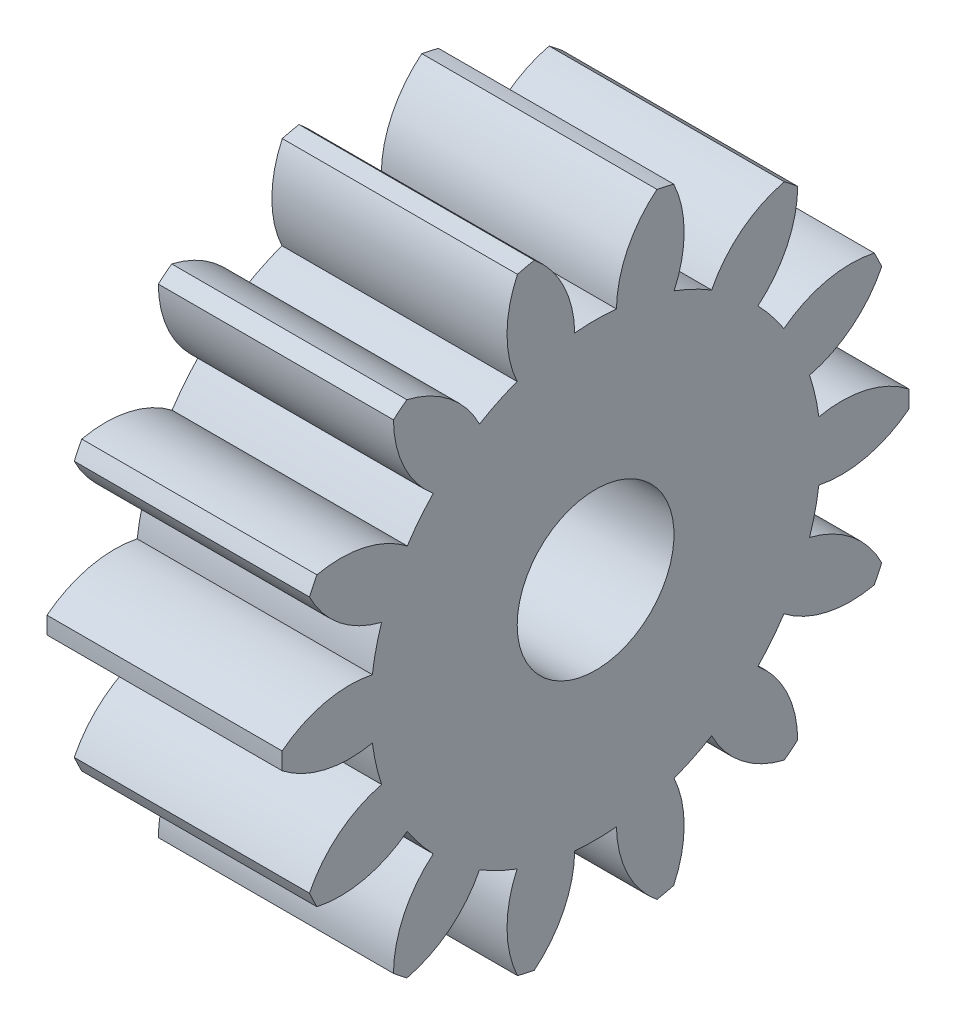
SolidWorks part; units mm, degrees
ref_plane "Plane1" through (0, 0, 0) normal (0, 0, 1) x (1, 0, 0)
ref_plane "Plane2" through (0, 0, 0) normal (0, 1, 0) x (1, 0, 0)
ref_plane "Plane3" through (0, 0, 0) normal (1, 0, 0) x (0, 0, -1)
sketch "HoldingSke" plane through (0, 0, 0) normal (0, 1, 0) x (1, 0, 0)
  line L0 (0, 0) -> (3.8812, -0.9677)
  line L1 (-15, 0) -> (100, 0) construction
  line L2 (0, 0) -> (-2.1039, 2.3779)
  line L3 (0, 0) -> (-11.863, 4.5341)
  line L4 (0, 0) -> (8.3795, 2.0892)
  line L5 (0, 0) -> (-46.8476, -17.4728)
  line L6 (0, 0) -> (-1.2434, -0.839)
  line L7 (-2.1039, 2.3779) -> (8.6586, 51.2059)
  line L8 (-76.2, 54.61) -> (-76.1, 54.61)
  line L9 (-71.009, 38.7566) -> (-53.1078, 45.2721)
  line L10 (-76.2, 71.12) -> (104.1128, 71.12)
  line L11 (0, 0) -> (-1.5, 0)
  line L12 (-76.2, 101.6) -> (-76.192, 101.6)
  line L13 (24.9733, 27.94) -> (52.9518, 28.4284)
  line L14 (24.9733, 27.94) -> (24.9743, 27.94)
  line L15 (24.9733, 27.94) -> (100.4006, 29.5858)
  line L16 (-63.627, -0.25) -> (-12.827, -0.25)
  circle A0 centre (0, 0) radius 0.5
  circle A1 centre (0, 0) radius 1.4365
  circle A2 centre (0, 0) radius 37.5
  circle A3 centre (0, 0) radius 0.5
  dimension "MHD" = 2.873
  dimension "Hub_dia" = 75
  dimension "Bore" = 1
  dimension "MBD" = 1
  dimension "Num_teeth" = 14
  dimension "Pitch" = 4
  dimension "Overall_len" = 50
  dimension "Show_teeth" = 14
  dimension "Thickness" = 1.5
  dimension "OAL" = 50.0001
  dimension "T_dim" = 0.1
  dimension "Ap" = 20
  dimension "H" = 19.05
  dimension "Pitch_radius" = 180.3128
  dimension "Width" = 1.5
  dimension "Backlash" = 0.008
  dimension "Addendum_fac" = 1
  dimension "Dedendum_fac" = 1.25
  dimension "Clearance_fac" = 0.25
  dimension "Dedendum_add" = 0.001
  dimension "Module" = 0.25
sketch "BasProSke" plane through (0, 0, 0) normal (0, 1, 0) x (1, 0, 0)
  line L0 (-10, 0) -> (60, 0) construction
  line L1 (0, 0) -> (0, 2)
  line L2 (0, 0) -> (1.5, 0)
  line L3 (1.5, 0) -> (1.5, 2)
  line L4 (1.5, 2) -> (0, 2)
  dimension "Thickness" = 1.5
  dimension "Diameter" = 4
revolve "Base-Revolve" add sketch "BasProSke" angle 360 about L0
sketch "TooCutSke" plane through (0, 0, 0) normal (1, 0, 0) x (0, 0, -1)
  line L1 (0, 0) -> (0, 107) construction
  line L2 (0, 0) -> (-0.2099, 1.7374) construction
  line L3 (0, 0) -> (-0.7746, 3.3938) construction
  line L4 (-0.2099, 1.7374) -> (-0.3873, 1.6969) construction
  arc A0 (0.1329, 1.4303) -> (-0.1329, 1.4303) centre (0, 0) ccw
  arc A1 (0.418, 1.9818) -> (-0.418, 1.9818) centre (0, 0) ccw
  circle A2 centre (0, 0) radius 1.75 construction
  circle A3 centre (0, 0) radius 1.6445 construction
  arc A4 (-0.1329, 1.4303) -> (-0.418, 1.9818) centre (-0.8328, 1.418) ccw
  arc A5 (0.418, 1.9818) -> (0.1329, 1.4303) centre (0.8328, 1.418) ccw
  dimension "Root_dia" = 2.873
  dimension "Overcut_dia" = 4.0508
  dimension "Pitch_dia" = 3.5
  dimension "Base_dia" = 3.2889
  dimension "Flank_rad" = 0.7
  dimension "Half_ang" = 12.857
  dimension "Half_CT" = 0.1819
extrude "ToothCut" cut sketch "TooCutSke" along normal through all
fillet "Breaks" [suppressed] radius 0.005
fillet "RootFillets" [suppressed] radius 0.0635
pattern_circular "TeethCuts" count 14 every 25.714 about axis through (-10, 0, 0) along (1, 0, 0) of "ToothCut", "RootFillets", "Breaks"
sketch "HubNeaOneSke" plane through (0, 0, 0) normal (-1, 0, 0) x (0, 0, 1)
  circle A0 centre (0, 0) radius 1.4365
  dimension "Diameter" = 2.873
extrude "HubNearOne" [suppressed] add sketch "HubNeaOneSke" along normal blind 48.5001
sketch "HubNeaBotSke" plane through (0, 0, 0) normal (-1, 0, 0) x (0, 0, 1)
  circle A0 centre (0, 0) radius 1.4365
  dimension "Diameter" = 2.873
extrude "HubNearBoth" [suppressed] add sketch "HubNeaBotSke" along normal blind 24.25
ref_plane "FarPln" through (1.5, 0, 0) normal (1, 0, 0) x (0, 0, -1)
sketch "HubFarSke" plane through (1.5, 0, 0) normal (1, 0, 0) x (0, 0, -1)
  circle A0 centre (0, 0) radius 1.4365
  dimension "Diameter" = 2.873
extrude "HubFar" [suppressed] add sketch "HubFarSke" along normal blind 24.25
sketch "BorSke" plane through (0, 0, 0) normal (1, 0, 0) x (0, 0, -1)
  circle A0 centre (0, 0) radius 0.5
  dimension "Diameter" = 1
extrude "Bore" cut sketch "BorSke" along normal mid plane 100.0001
sketch "KeySke" plane through (0, 0, 0) normal (1, 0, 0) x (0, 0, -1)
  line L0 (-0.05, 0) -> (-0.05, 0.6)
  line L1 (-0.05, 0.6) -> (0.05, 0.6)
  line L2 (0.05, 0.6) -> (0.05, 0)
  line L3 (0, 0) -> (0, 34) construction
  line L4 (-0.05, 0) -> (0.05, 0)
  dimension "Offset" = 0.6
  dimension "Width" = 0.1
extrude "Keyway" [suppressed] cut sketch "KeySke" along normal mid plane 100.0001
pattern_circular "Keyway2" [suppressed] count 2 every 90 about axis through (-10, 0, 0) along (1, 0, 0)
equation "' \"Module@HoldingSke\" = 6.35"
equation "' \"Num_teeth@HoldingSke\" = 12"
equation "' \"Ap@HoldingSke\" =  20"
equation "' \"Ap@HoldingSke\" = 20"
equation "' \"Width@HoldingSke\" = 0.5 * 25.4"
equation "' \"Hub_dia@HoldingSke\"= 1 * 25.4"
equation "' \"Hub_dia@HoldingSke\" = 1 * 25.4"
equation "' \"Overall_len@HoldingSke\" = 1.0 * 25.4"
equation "' \"Bore@HoldingSke\" = 0.75 * 25.4"
equation "' \"T_dim@HoldingSke\" = 0.1 * 25.4"
equation "' \"Width@KeySke\" = 0.25 * 25.4"
equation "' \"Show_teeth@HoldingSke\" = 13"
equation "' \"Backlash@HoldingSke\" = 0.009 * 25.4"
equation "' \"Addendum_fac@HoldingSke\" = 1.0"
equation "' \"Dedendum_fac@HoldingSke\" = 1.25"
equation "' \"Dedendum_add@HoldingSke\" = 0.00005 * 25.4"
equation "' \"Clearance_fac@HoldingSke\" = 0.25"
equation "\"Pitch@HoldingSke\" = 1 / \"Module@HoldingSke\""
equation "\"Overcut_dia@TooCutSke\" = (\"Num_teeth@HoldingSke\" + 2 * \"Addendum_fac@HoldingSke\") / \"Pitch@HoldingSke\" + 0.002 * 25.4"
equation "\"Pitch_dia@TooCutSke\" = \"Num_teeth@HoldingSke\" / \"Pitch@HoldingSke\""
equation "\"Base_dia@TooCutSke\" = \"Num_teeth@HoldingSke\" / \"Pitch@HoldingSke\" * cos((\"Ap@HoldingSke\"  * 3.14159265 / 180))"
equation "\"Root_dia@TooCutSke\" = (\"Num_teeth@HoldingSke\" + 2) / \"Pitch@HoldingSke\" - 2 * (\"Addendum_fac@HoldingSke\" + \"Dedendum_fac@HoldingSke\") / \"Pitch@HoldingSke\" - \"Dedendum_add@HoldingSke\" * 2"
equation "\"Half_ang@TooCutSke\" = 180 / \"Num_teeth@HoldingSke\""
equation "\"Half_CT@TooCutSke\" = \"Num_teeth@HoldingSke\" / \"Pitch@HoldingSke\" * sin((3.14159265 / 2 / \"Num_teeth@HoldingSke\")) / 2 - 7 * \"Backlash@HoldingSke\" / 4"
equation "\"Flank_rad@TooCutSke\" = \"Num_teeth@HoldingSke\" / \"Pitch@HoldingSke\" / 5"
equation "\"Radius@RootFillets\" = \"Clearance_fac@HoldingSke\" / \"Pitch@HoldingSke\" + \"Dedendum_add@HoldingSke\""
equation "\"Break_rad@Breaks\" = 0.02 / \"Pitch@HoldingSke\""
equation "\"Thickness@HoldingSke\" = \"Width@HoldingSke\""
equation "\"OAL@HoldingSke\" = \"Thickness@HoldingSke\""
equation "\"MHD@HoldingSke\" = (\"Num_teeth@HoldingSke\" + 2) / \"Pitch@HoldingSke\" - 2 * (\"Addendum_fac@HoldingSke\" + \"Dedendum_fac@HoldingSke\")  / \"Pitch@HoldingSke\" - \"Dedendum_add@HoldingSke\" * 2"
equation "\"MBD@HoldingSke\" = (\"Num_teeth@HoldingSke\" + 2) / \"Pitch@HoldingSke\" - 2 * (\"Addendum_fac@HoldingSke\" + \"Dedendum_fac@HoldingSke\")  / \"Pitch@HoldingSke\" - \"Dedendum_add@HoldingSke\" * 2 - 0.002 * 25.4"
equation "\"MHD@HoldingSke\" = ((sgn( \"MHD@HoldingSke\" - \"Hub_dia@HoldingSke\" )-1)*( \"MHD@HoldingSke\" - \"Hub_dia@HoldingSke\" ))/-2+ \"Hub_dia@HoldingSke\""
equation "\"MBD@HoldingSke\" = ((sgn( \"MBD@HoldingSke\" - \"Bore@HoldingSke\" )-1)*( \"MBD@HoldingSke\" - \"Bore@HoldingSke\" ))/-2+ \"Bore@HoldingSke\""
equation "\"OAL@HoldingSke\" = ((sgn( \"OAL@HoldingSke\" - \"Overall_len@HoldingSke\" )+1)*( \"OAL@HoldingSke\" - \"Overall_len@HoldingSke\" ))/2 + \"Overall_len@HoldingSke\" + 0.000002 * 25.4"
equation "\"Num_teeth@TeethCuts\" = int( \"Show_teeth@HoldingSke\" ) + 1"
equation "\"Num_teeth@TeethCuts\" = ((sgn( \"Num_teeth@TeethCuts\" - \"Num_teeth@HoldingSke\" )-1)*( \"Num_teeth@TeethCuts\" - \"Num_teeth@HoldingSke\" ))/-2+ \"Num_teeth@HoldingSke\""
equation "\"Num_teeth@TeethCuts\" = ((sgn( \"Num_teeth@TeethCuts\" - 2.0)+1)*( \"Num_teeth@TeethCuts\" - 2.0))/2 +2.0"
equation "\"Angle@TeethCuts\" = 360.0 / \"Num_teeth@HoldingSke\""
equation "\"Diameter@BasProSke\" = (\"Num_teeth@HoldingSke\" + 2 * \"Addendum_fac@HoldingSke\") / \"Pitch@HoldingSke\""
equation "\"Thickness@BasProSke\"  = \"Thickness@HoldingSke\""
equation "' \"Fillet_rad@BasProSke\" =  \"Thickness@HoldingSke\" * 0.05"
equation "' \"Fillet_rad@BasProSke\" = \"Thickness@HoldingSke\" * 0.05"
equation "\"MHD@HoldingSke\" = ((sgn( \"MHD@HoldingSke\" - \"Root_dia@TooCutSke\" )-1)*( \"MHD@HoldingSke\" - \"Root_dia@TooCutSke\" ))/-2+ \"Root_dia@TooCutSke\""
equation "\"Diameter@HubNeaOneSke\" = \"MHD@HoldingSke\""
equation "\"Length@HubNearOne\" = \"OAL@HoldingSke\" - \"Thickness@BasProSke\""
equation "\"Diameter@HubNeaBotSke\" = \"MHD@HoldingSke\""
equation "\"Length@HubNearBoth\" = ( \"OAL@HoldingSke\" - \"Thickness@BasProSke\" ) / 2.0"
equation "\"Thickness@FarPln\" = \"Thickness@BasProSke\""
equation "\"Diameter@HubFarSke\" = \"MHD@HoldingSke\""
equation "\"Length@HubFar\" = ( \"OAL@HoldingSke\" - \"Thickness@BasProSke\" ) / 2.0"
equation "\"Diameter@BorSke\" = \"MBD@HoldingSke\""
equation "\"D1@Bore\" = \"OAL@HoldingSke\" * 2.0"
equation "\"D1@Keyway\" = \"OAL@HoldingSke\" * 2.0"
equation "\"Offset@KeySke\" = \"T_dim@HoldingSke\" + \"MBD@HoldingSke\" / 2.0"
